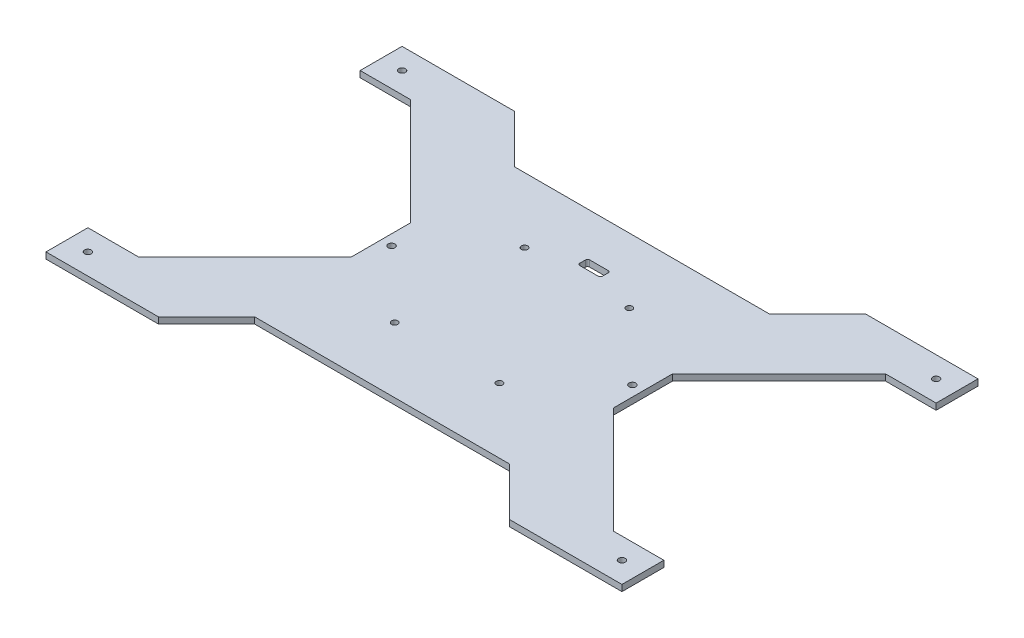
SolidWorks part; units mm, degrees
material "Thornel Mat VMA"
ref_plane "Front Plane" through (0, 0, 0) normal (0, 0, 1) x (1, 0, 0)
ref_plane "Top Plane" through (0, 0, 0) normal (0, 1, 0) x (1, 0, 0)
ref_plane "Right Plane" through (0, 0, 0) normal (1, 0, 0) x (0, 0, -1)
sketch "Sketch1" plane through (0, 0, 0) normal (0, -1, 0) x (1, 0, 0)
  line L0 (2.6321, -227.497) -> (-21.5101, -227.497)
  line L1 (-21.5101, -282.497) -> (-21.5101, 7.503) construction
  line L2 (-21.5101, -227.497) -> (-21.5101, -207.497)
  line L3 (-21.5101, -207.497) -> (32.1295, -207.497)
  line L4 (32.1295, -207.497) -> (55.0921, -230.4596)
  line L5 (55.0921, -230.4596) -> (176.8877, -230.4596)
  line L6 (53.4899, -292.497) -> (115.9899, -292.497) construction
  line L7 (115.9899, -230.4596) -> (115.9899, -292.497) construction
  line L8 (178.4899, -278.3549) -> (178.4899, -306.6392)
  line L9 (229.3478, -227.497) -> (178.4899, -278.3549)
  line L10 (253.4899, -227.497) -> (229.3478, -227.497)
  line L11 (253.4899, -207.497) -> (253.4899, -227.497)
  line L12 (199.8503, -207.497) -> (176.8877, -230.4596)
  line L13 (253.4899, -207.497) -> (199.8503, -207.497)
  line L14 (253.4899, -227.497) -> (253.4899, -207.497)
  line L15 (229.3478, -227.497) -> (253.4899, -227.497)
  line L16 (2.6321, -357.497) -> (53.4899, -306.6392)
  line L17 (-21.5101, -357.497) -> (2.6321, -357.497)
  line L18 (-21.5101, -377.497) -> (-21.5101, -357.497)
  line L19 (229.3478, -357.497) -> (253.4899, -357.497)
  line L20 (253.4899, -357.497) -> (253.4899, -377.497)
  line L21 (253.4899, -377.497) -> (199.8503, -377.497)
  line L22 (199.8503, -377.497) -> (176.8877, -354.5345)
  line L23 (253.4899, -377.497) -> (253.4899, -357.497)
  line L24 (253.4899, -357.497) -> (229.3478, -357.497)
  line L25 (229.3478, -357.497) -> (178.4899, -306.6392)
  line L26 (55.0921, -354.5345) -> (176.8877, -354.5345)
  line L27 (-21.5101, -357.497) -> (-21.5101, -377.497)
  line L28 (-21.5101, -377.497) -> (10.9163, -377.497)
  line L29 (-21.5101, -377.497) -> (10.9163, -377.497)
  line L30 (10.9163, -377.497) -> (53.9163, -334.497)
  line L31 (10.9163, -377.497) -> (53.9163, -334.497) construction
  line L32 (53.9163, -334.497) -> (178.0635, -334.497)
  line L33 (253.4899, -377.497) -> (253.4899, -357.497)
  line L34 (253.4899, -357.497) -> (229.3478, -357.497)
  line L35 (229.3478, -357.497) -> (178.4899, -306.6392)
  line L36 (178.4899, -306.6392) -> (178.4899, -278.3549)
  line L37 (178.4899, -278.3549) -> (229.3478, -227.497)
  line L38 (229.3478, -227.497) -> (253.4899, -227.497)
  line L39 (253.4899, -227.497) -> (253.4899, -152.7096)
  line L40 (253.4899, -152.7096) -> (229.3478, -152.7096)
  line L41 (53.9163, -334.497) -> (178.0635, -334.497) construction
  line L42 (178.0635, -334.497) -> (221.0635, -377.497)
  line L43 (178.0635, -334.497) -> (221.0635, -377.497) construction
  line L44 (2.6321, -152.7096) -> (-21.5101, -152.7096)
  line L45 (-21.5101, -152.7096) -> (-21.5101, -227.497)
  line L46 (-21.5101, -227.497) -> (2.6321, -227.497)
  line L47 (2.6321, -227.497) -> (53.4899, -278.3549)
  line L48 (53.4899, -278.3549) -> (53.4899, -306.6392)
  line L49 (53.4899, -306.6392) -> (2.6321, -357.497)
  line L50 (2.6321, -357.497) -> (-21.5101, -357.497)
  line L69 (-21.5101, -207.497) -> (-21.5101, -227.497)
  line L70 (-21.5101, -227.497) -> (2.6321, -227.497)
  line L71 (2.6321, -227.497) -> (53.4899, -278.3549)
  line L72 (53.4899, -278.3549) -> (53.4899, -306.6392)
  line L75 (32.1295, -377.497) -> (55.0921, -354.5345)
  line L76 (-21.5101, -377.497) -> (32.1295, -377.497)
  line L77 (-21.5101, -357.497) -> (-21.5101, -377.497)
  line L78 (2.6321, -357.497) -> (-21.5101, -357.497)
  line L127 (221.0635, -377.497) -> (253.4899, -377.497)
  line L128 (221.0635, -377.497) -> (253.4899, -377.497)
  line L129 (229.3478, -152.7096) -> (189.3478, -112.7096)
  line L130 (229.3478, -152.7096) -> (189.3478, -112.7096)
  line L131 (189.3478, -112.7096) -> (42.6321, -112.7096)
  line L132 (189.3478, -112.7096) -> (42.6321, -112.7096)
  line L133 (42.6321, -112.7096) -> (2.6321, -152.7096)
  line L134 (42.6321, -112.7096) -> (2.6321, -152.7096)
  circle A0 centre (-11.5101, -217.497) radius 1.6
  circle A1 centre (243.4899, -217.497) radius 1.6
  circle A2 centre (243.4899, -367.497) radius 1.6
  circle A3 centre (-11.5101, -367.497) radius 1.6
  circle A4 centre (58.4899, -292.497) radius 1.6
  circle A5 centre (173.4899, -292.497) radius 1.6
  point P50 (178.4899, -292.497)
  line M31 (-1.5101, -302.497) -> (233.4899, -302.497)
  line M32 (233.4899, -302.497) -> (233.4899, -592.497)
  line M34 (-1.5101, -592.497) -> (-1.5101, -302.497)
  line M35 (233.4899, -282.497) -> (-1.5101, -282.497)
  line M36 (-1.5101, -282.497) -> (-1.5101, 7.503)
  line M38 (233.4899, 7.503) -> (233.4899, -282.497)
  line M39 (-21.5101, 7.503) -> (-21.5101, -282.497)
  line M43 (-21.5101, -302.497) -> (-21.5101, -592.497)
  line M49 (253.4899, -592.497) -> (253.4899, -302.497)
  line M53 (253.4899, -282.497) -> (253.4899, 7.503)
  dimension "D4" = 3.2
  dimension "D5" = 5
  dimension "D6" = 5
  dimension "D2" = 20
  dimension "D3" = 35
  dimension "D1" = 0
extrude "Extrude2" add sketch "Sketch1" along normal blind 3 contours L76 L17 A3 M43 M34 | L76 L75 L26 L22 L21 L19 L25 L8 L72 L16 L17 M34 M32 M31 | L21 L19 A2 M49 M32 | L72 L8 A5 A4 M35 M31 | L71 L72 L8 L9 L10 L13 L12 L5 L4 L3 L0 M35 M38 M36 | L3 L0 A0 M39 M36 | L13 L10 A1 M53 M38
sketch "Sketch4" plane through (0, -3, 0) normal (0, -1, 0) x (1, 0, 0)
  line L0 (121.3899, -332.9844) -> (121.3899, -330.2844) construction
  line L1 (120.3899, -329.2844) -> (111.5899, -329.2844) construction
  line L2 (111.5899, -333.9844) -> (120.3899, -333.9844) construction
  line L3 (110.5899, -330.2844) -> (110.5899, -332.9844) construction
  line L4 (121.3899, -332.9844) -> (121.3899, -330.2844)
  line L5 (120.3899, -329.2844) -> (111.5899, -329.2844)
  line L6 (111.5899, -333.9844) -> (120.3899, -333.9844)
  line L7 (110.5899, -330.2844) -> (110.5899, -332.9844)
  arc A0 (121.3899, -330.2844) -> (120.3899, -329.2844) centre (120.3899, -330.2844) ccw construction
  arc A1 (120.3899, -333.9844) -> (121.3899, -332.9844) centre (120.3899, -332.9844) ccw construction
  arc A2 (110.5899, -332.9844) -> (111.5899, -333.9844) centre (111.5899, -332.9844) ccw construction
  arc A3 (111.5899, -329.2844) -> (110.5899, -330.2844) centre (111.5899, -330.2844) ccw construction
  arc A4 (142.4899, -261.497) -> (139.4899, -261.497) centre (140.9899, -261.497) ccw construction
  arc A5 (139.4899, -261.497) -> (142.4899, -261.497) centre (140.9899, -261.497) ccw construction
  arc A6 (139.4899, -323.497) -> (142.4899, -323.497) centre (140.9899, -323.497) ccw construction
  arc A7 (142.4899, -323.497) -> (139.4899, -323.497) centre (140.9899, -323.497) ccw construction
  arc A8 (92.4899, -261.497) -> (89.4899, -261.497) centre (90.9899, -261.497) ccw construction
  arc A9 (89.4899, -261.497) -> (92.4899, -261.497) centre (90.9899, -261.497) ccw construction
  arc A10 (92.4899, -323.497) -> (89.4899, -323.497) centre (90.9899, -323.497) ccw construction
  arc A11 (89.4899, -323.497) -> (92.4899, -323.497) centre (90.9899, -323.497) ccw construction
  arc A12 (121.3899, -330.2844) -> (120.3899, -329.2844) centre (120.3899, -330.2844) ccw
  arc A13 (120.3899, -333.9844) -> (121.3899, -332.9844) centre (120.3899, -332.9844) ccw
  arc A14 (110.5899, -332.9844) -> (111.5899, -333.9844) centre (111.5899, -332.9844) ccw
  arc A15 (111.5899, -329.2844) -> (110.5899, -330.2844) centre (111.5899, -330.2844) ccw
  arc A16 (142.4899, -261.497) -> (139.4899, -261.497) centre (140.9899, -261.497) ccw
  arc A17 (139.4899, -261.497) -> (142.4899, -261.497) centre (140.9899, -261.497) ccw
  arc A18 (139.4899, -323.497) -> (142.4899, -323.497) centre (140.9899, -323.497) ccw
  arc A19 (142.4899, -323.497) -> (139.4899, -323.497) centre (140.9899, -323.497) ccw
  arc A20 (92.4899, -261.497) -> (89.4899, -261.497) centre (90.9899, -261.497) ccw
  arc A21 (89.4899, -261.497) -> (92.4899, -261.497) centre (90.9899, -261.497) ccw
  arc A22 (92.4899, -323.497) -> (89.4899, -323.497) centre (90.9899, -323.497) ccw
  arc A23 (89.4899, -323.497) -> (92.4899, -323.497) centre (90.9899, -323.497) ccw
extrude "Cut-Extrude4" cut sketch "Sketch4" against normal blind 3
